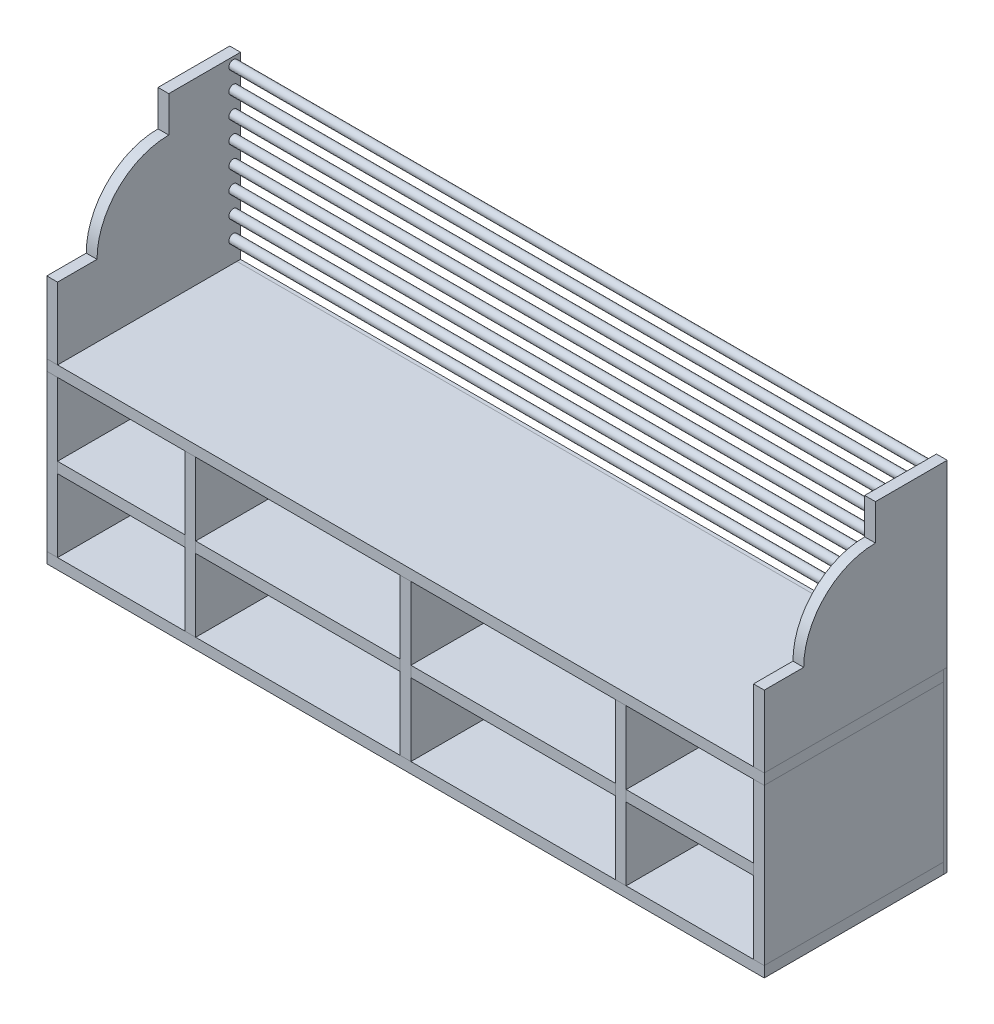
SolidWorks part; units mm, degrees
ref_plane "Front Plane" through (0, 0, 0) normal (0, 0, 1) x (1, 0, 0)
ref_plane "Top Plane" through (0, 0, 0) normal (0, 1, 0) x (1, 0, 0)
ref_plane "Right Plane" through (0, 0, 0) normal (1, 0, 0) x (0, 0, -1)
sketch "Sketch1" plane through (0, 0, 0) normal (0, 0, 1) x (1, 0, 0)
  line L0 (0, 0) -> (0, -197528.1558) construction
  line L1 (0, 0) -> (-197528.1558, 0) construction
  line L3 (-1000, -15) -> (1000, -15)
  line L4 (-1000, -15) -> (-1000, 15)
  line L5 (-1000, 15) -> (1000, 15)
  line L6 (1000, -15) -> (1000, 15)
  line L7 (-1000, -15) -> (1000, 15) construction
  line L8 (-1000, 15) -> (1000, -15) construction
  point P5 (0, 0)
  dimension "D1" = 2000
  dimension "D2" = 30
extrude "Boss-Extrude1" add sketch "Sketch1" along normal mid plane 500
move or copy body "Body-Move/Copy1" bodies to move or copy 101 copy yes number of copies 1 translate (0, 465, 0)
sketch "Sketch3" plane through (0, 0, 250) normal (0, 0, 1) x (1, 0, 0)
  line L0 (1000, 15) -> (-1000, 15) construction
  line L1 (-1000, 450) -> (-970, 450)
  line L2 (-1000, 450) -> (-1000, 15)
  line L3 (-1000, 15) -> (-970, 15)
  line L4 (-970, 450) -> (-970, 15)
  line L5 (-1000, 450) -> (1000, 450) construction
  line L6 (-615, 450) -> (-585, 450)
  line L7 (-615, 450) -> (-615, 15)
  line L8 (-615, 15) -> (-585, 15)
  line L9 (-585, 450) -> (-585, 15)
  line L10 (0, -107.9237) -> (0, 542.9162) construction
  line L11 (-15, 450) -> (15, 450)
  line L12 (-15, 450) -> (-15, 15)
  line L13 (-15, 15) -> (15, 15)
  line L14 (15, 450) -> (15, 15)
  line L15 (615, 15) -> (585, 15)
  line L16 (615, 450) -> (585, 450)
  line L17 (1000, 15) -> (970, 15)
  line L18 (1000, 450) -> (970, 450)
  line L19 (585, 450) -> (585, 15)
  line L20 (615, 450) -> (615, 15)
  line L21 (970, 450) -> (970, 15)
  line L22 (1000, 450) -> (1000, 15)
  point P17 (-1000, 232.5)
  dimension "D1" = 30
  dimension "D2" = 355
  dimension "D3" = 570
extrude "Boss-Extrude3" add sketch "Sketch3" against normal blind 500 separate body
sketch "Sketch6" plane through (0, 0, 250) normal (0, 0, 1) x (1, 0, 0)
  line L0 (-1000, 232.5) -> (1000, 232.5) construction
  line L1 (-1000, 450) -> (-1000, 15) construction
  line L2 (1000, 15) -> (1000, 450) construction
  line L3 (-970, 15) -> (-970, 450) construction
  line L4 (-970, 247.5) -> (-615, 247.5)
  line L5 (-970, 247.5) -> (-970, 217.5)
  line L6 (-970, 217.5) -> (-615, 217.5)
  line L7 (-615, 247.5) -> (-615, 217.5)
  line L8 (-615, 450) -> (-615, 15) construction
  line L9 (-585, 15) -> (-585, 450) construction
  line L10 (-585, 247.5) -> (-15, 247.5)
  line L11 (-585, 247.5) -> (-585, 217.5)
  line L12 (-585, 217.5) -> (-15, 217.5)
  line L13 (-15, 247.5) -> (-15, 217.5)
  line L14 (-15, 450) -> (-15, 15) construction
  line L15 (15, 15) -> (15, 450) construction
  line L16 (15, 247.5) -> (585, 247.5)
  line L17 (15, 247.5) -> (15, 217.5)
  line L18 (15, 217.5) -> (585, 217.5)
  line L19 (585, 247.5) -> (585, 217.5)
  line L20 (585, 450) -> (585, 15) construction
  line L21 (615, 15) -> (615, 450) construction
  line L22 (615, 247.5) -> (970, 247.5)
  line L23 (615, 247.5) -> (615, 217.5)
  line L24 (615, 217.5) -> (970, 217.5)
  line L25 (970, 247.5) -> (970, 217.5)
  line L26 (970, 450) -> (970, 15) construction
  dimension "D1" = 30
extrude "Boss-Extrude6" add sketch "Sketch6" against normal blind 500 separate body
sketch "Sketch7" plane through (0, 0, -250) normal (0, 0, -1) x (-1, 0, 0)
  line L1 (-1000, 480) -> (1000, 480)
  line L2 (-1000, 480) -> (-1000, -15)
  line L3 (-1000, -15) -> (1000, -15)
  line L4 (1000, 480) -> (1000, -15)
extrude "Boss-Extrude7" add sketch "Sketch7" along normal blind 10 separate body
sketch "Sketch8" plane through (1000, 0, 0) normal (1, 0, 0) x (0, 0, -1)
  line L0 (-250, 480) -> (-250, 680)
  line L1 (-250, 680) -> (-140, 680)
  line L2 (60, 880) -> (60, 980)
  line L3 (60, 980) -> (260, 980)
  line L4 (260, 980) -> (260, 480)
  line L5 (260, 480) -> (-250, 480)
  arc A0 (-140, 680) -> (60, 880) centre (60, 680) cw
  dimension "D3" = 200
  dimension "D1" = 200
  dimension "D2" = 500
  dimension "D4" = 200
extrude "Boss-Extrude8" add sketch "Sketch8" against normal blind 30 separate body
move or copy body "Body-Move/Copy2" bodies to move or copy 126 copy yes number of copies 1 translate (-1970, 0, 0)
sketch "Sketch11" plane through (970, 0, 0) normal (-1, 0, 0) x (0, 0, 1)
  line L0 (-260, 480) -> (-260, 980) construction
  line L1 (-260, 980) -> (-60, 980) construction
  line L2 (-260, 480) -> (-260, 980) construction
  circle A0 centre (-240, 960) radius 12.5
  circle A1 centre (-240, 900) radius 12.5
  circle A2 centre (-240, 840) radius 12.5
  circle A3 centre (-240, 780) radius 12.5
  circle A4 centre (-240, 720) radius 12.5
  circle A5 centre (-240, 660) radius 12.5
  circle A6 centre (-240, 600) radius 12.5
  circle A7 centre (-240, 540) radius 12.5
  point P22 (0, 0)
  dimension "D1" = 25
  dimension "D2" = 20
  dimension "D3" = 20
  dimension "D5" = 20
  dimension "D6" = 60
  dimension "D4" = 8
extrude "Boss-Extrude10" add sketch "Sketch11" along normal up to next (1970 mm away)
